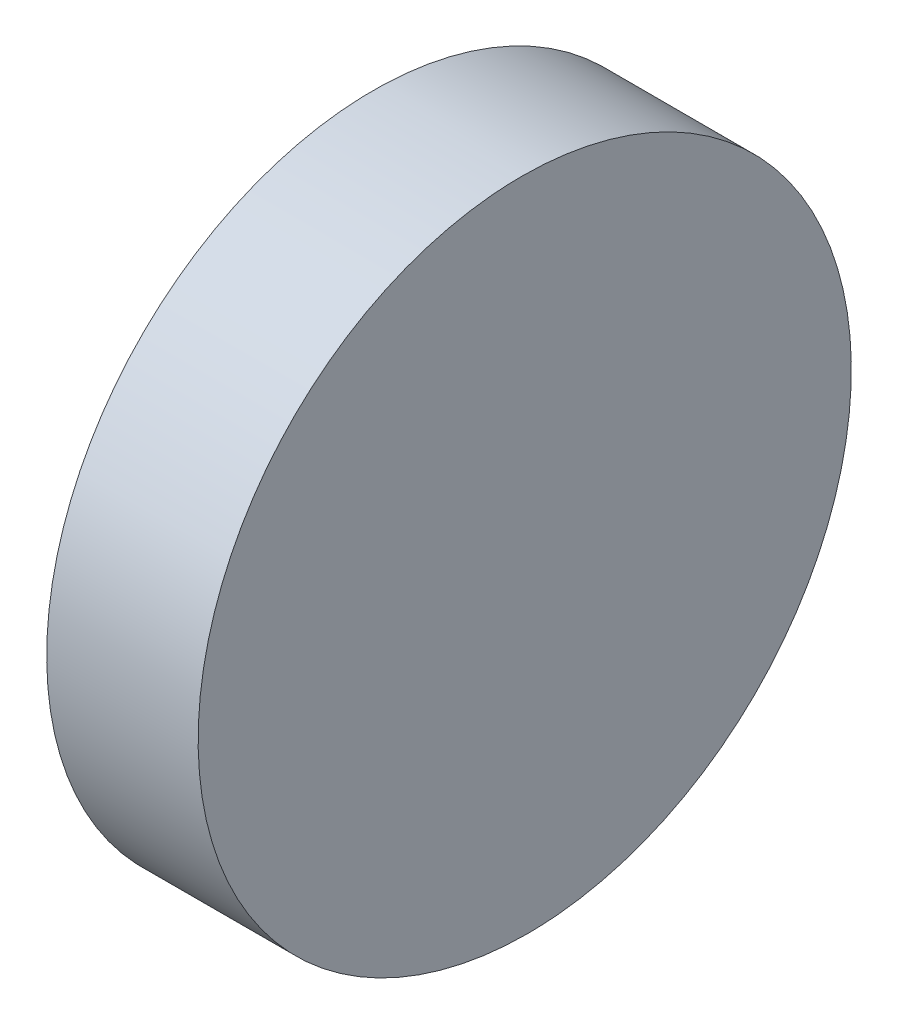
SolidWorks part; units mm, degrees
ref_plane "前视基准面" through (0, 0, 0) normal (0, 0, 1) x (1, 0, 0)
ref_plane "上视基准面" through (0, 0, 0) normal (0, 1, 0) x (1, 0, 0)
ref_plane "右视基准面" through (0, 0, 0) normal (1, 0, 0) x (0, 0, -1)
sketch "草图1" plane through (0, 0, 0) normal (0, 0, 1) x (1, 0, 0)
  line L0 (15.2768, 0) -> (-15.2768, 0) construction
  line L1 (0, 12.7) -> (0, -12.7)
  line L2 (0, -12.7) -> (6, -12.7)
  line L3 (6, -12.7) -> (5.7783, 12.7)
  line L4 (0, 12.7) -> (5.7783, 12.7)
  point P5 (0, 0)
  dimension "D1" = 6
  dimension "D2" = 25.4
  dimension "D3" = 0.5
extrude "凸台-拉伸1" add sketch "草图1" along normal blind 25.4 contours L1 L2 L3 L4
sketch "草图2" plane through (0, 0, 0) normal (-1, 0, 0) x (0, 0, 1)
  line L4 (0, 12.7) -> (0, -12.7)
  line L5 (0, -12.7) -> (25.4, -12.7)
  line L6 (25.4, -12.7) -> (25.4, 12.7)
  line L7 (25.4, 12.7) -> (0, 12.7)
  line L8 (0, 12.7) -> (0, -12.7)
  line L9 (0, -12.7) -> (25.4, -12.7)
  line L10 (25.4, -12.7) -> (25.4, 12.7)
  line L11 (25.4, 12.7) -> (0, 12.7)
  circle A0 centre (12.7, 0) radius 12.7
  point P7 (12.7, 12.7)
  line M1 (0, 12.7) -> (0, -12.7)
  line M2 (0, -12.7) -> (25.4, -12.7)
  line M3 (25.4, -12.7) -> (25.4, 12.7)
  line M4 (25.4, 12.7) -> (0, 12.7)
  dimension "D2" = 25.4
  dimension "D1" = 0
extrude "切除-拉伸1" cut sketch "草图2" against normal blind 10 contours A0 L8 M2 | A0 L9 M3 | A0 L10 M4 | A0 L11 M1
